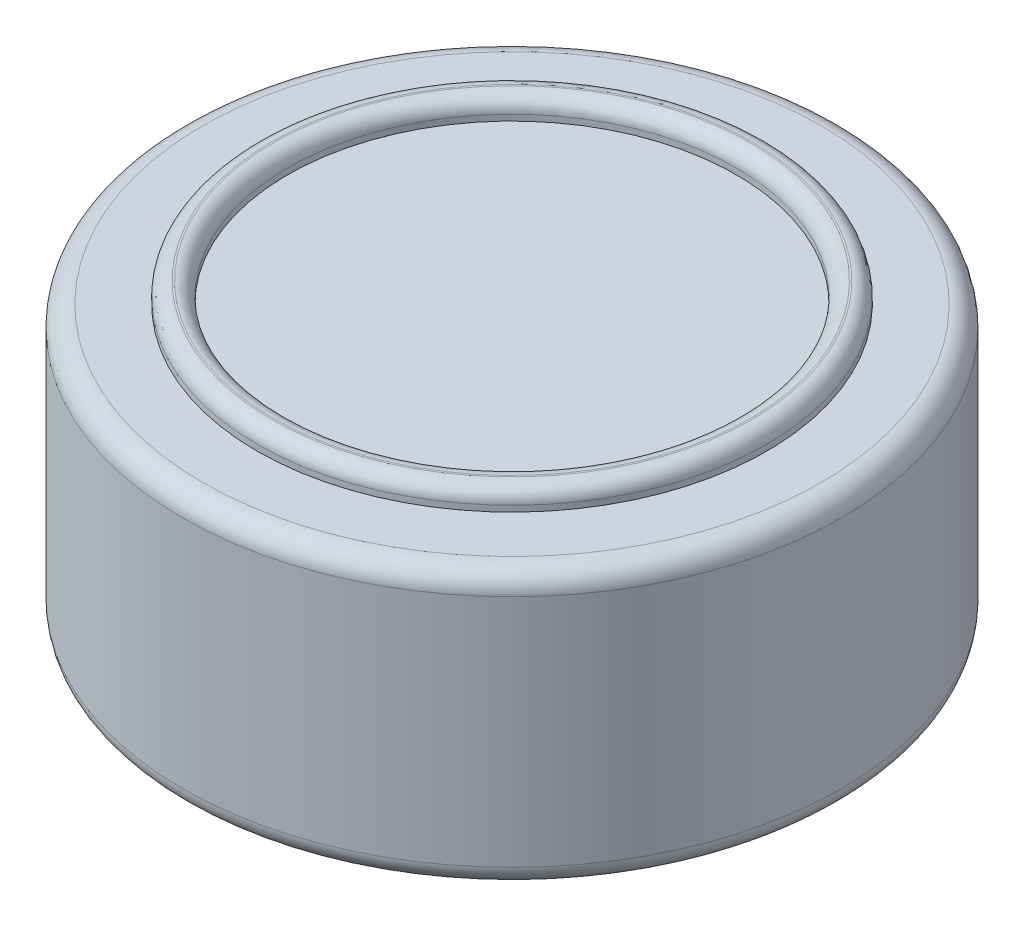
SolidWorks part; units mm, degrees
ref_plane "Front" through (0, 0, 0) normal (0, 0, 1) x (1, 0, 0)
ref_plane "Top" through (0, 0, 0) normal (0, 1, 0) x (1, 0, 0)
ref_plane "Right" through (0, 0, 0) normal (1, 0, 0) x (0, 0, -1)
sketch "Sketch1" plane through (0, 0, 0) normal (0, 1, 0) x (1, 0, 0)
  circle A0 centre (0, 0) radius 16.1655
  dimension "D1" = 32.331
extrude "Boss-Extrude1" add sketch "Sketch1" along normal blind 13.5 contours A0
fillet "Fillet1" radius 1 2 edges at (0, 0, 16.1655) (0, 13.5, 16.1655)
sketch "Sketch2" plane through (0, 13.5, 0) normal (0, 1, 0) x (1, 0, 0)
  circle A0 centre (0, 0) radius 12.5
  circle A1 centre (0, 0) radius 11
  dimension "D1" = 25
  dimension "D2" = 22
extrude "Boss-Extrude2" add sketch "Sketch2" along normal blind 1
fillet "Fillet4" radius 0.707 2 edges at (0, 14.5, 11) (0, 14.5, 12.5)
